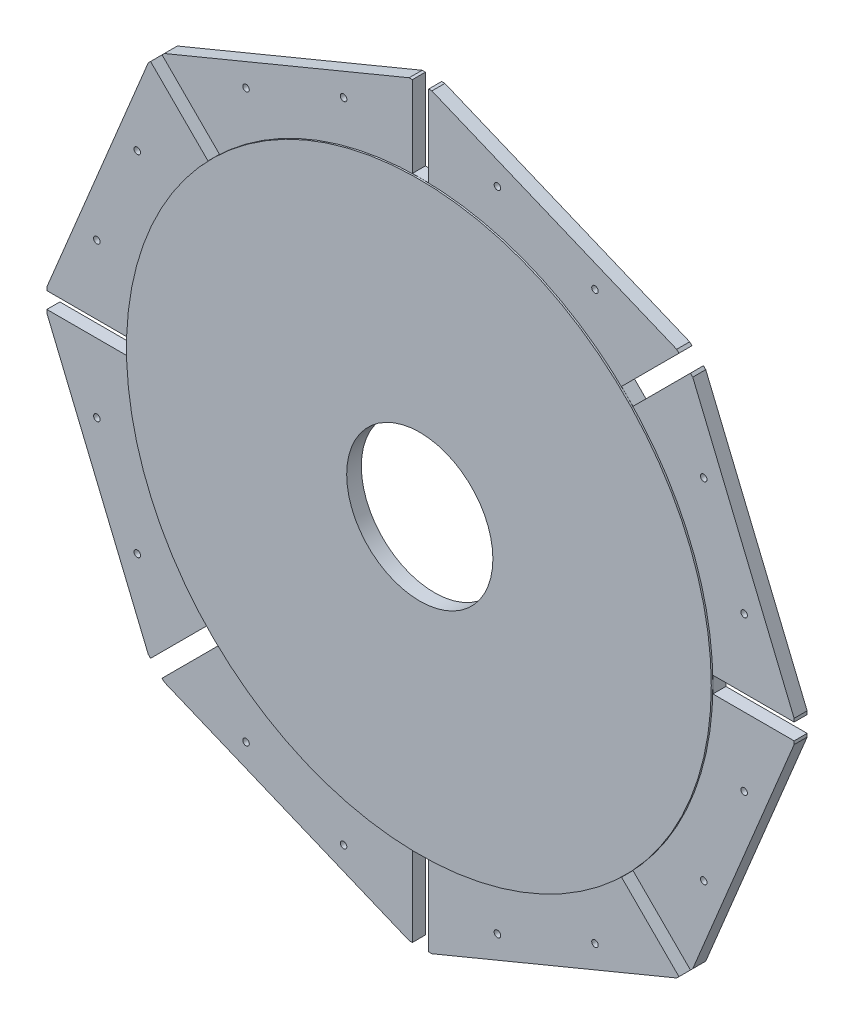
SolidWorks part; units mm, degrees
ref_plane "Front Plane" through (0, 0, 0) normal (0, 0, 1) x (1, 0, 0)
ref_plane "Top Plane" through (0, 0, 0) normal (0, 1, 0) x (1, 0, 0)
ref_plane "Right Plane" through (0, 0, 0) normal (1, 0, 0) x (0, 0, -1)
sketch "Sketch1" plane through (0, 0, 0) normal (0, 0, 1) x (1, 0, 0)
  line L0 (5, 230) -> (5, 180)
  line L1 (5, 180) -> (-5, 180)
  line L2 (-5, 180) -> (-5, 230)
  line L3 (-5, 230) -> (-7, 230)
  line L4 (-7, 230) -> (-157.6848, 167.5843)
  line L5 (-157.6848, 167.5843) -> (-159.099, 166.1701)
  line L6 (-159.099, 166.1701) -> (-123.7437, 130.8148)
  line L7 (-123.7437, 130.8148) -> (-130.8148, 123.7437)
  line L8 (-130.8148, 123.7437) -> (-166.1701, 159.099)
  line L9 (-166.1701, 159.099) -> (-167.5843, 157.6848)
  line L10 (-167.5843, 157.6848) -> (-230, 7)
  line L11 (-230, 7) -> (-230, 5)
  line L12 (-230, 5) -> (-180, 5)
  line L13 (-180, 5) -> (-180, -5)
  line L14 (-180, -5) -> (-230, -5)
  line L15 (-230, -5) -> (-230, -7)
  line L16 (-230, -7) -> (-167.5843, -157.6848)
  line L17 (-167.5843, -157.6848) -> (-166.1701, -159.099)
  line L18 (-166.1701, -159.099) -> (-130.8148, -123.7437)
  line L19 (-130.8148, -123.7437) -> (-123.7437, -130.8148)
  line L20 (-123.7437, -130.8148) -> (-159.099, -166.1701)
  line L21 (-159.099, -166.1701) -> (-157.6848, -167.5843)
  line L22 (-157.6848, -167.5843) -> (-7, -230)
  line L23 (-7, -230) -> (-5, -230)
  line L24 (-5, -230) -> (-5, -180)
  line L25 (-5, -180) -> (5, -180)
  line L26 (5, -180) -> (5, -230)
  line L27 (5, -230) -> (7, -230)
  line L28 (7, -230) -> (157.6848, -167.5843)
  line L29 (157.6848, -167.5843) -> (159.099, -166.1701)
  line L30 (159.099, -166.1701) -> (123.7437, -130.8148)
  line L31 (123.7437, -130.8148) -> (130.8148, -123.7437)
  line L32 (130.8148, -123.7437) -> (166.1701, -159.099)
  line L33 (166.1701, -159.099) -> (167.5843, -157.6848)
  line L34 (167.5843, -157.6848) -> (230, -7)
  line L35 (230, -7) -> (230, -5)
  line L36 (230, -5) -> (180, -5)
  line L37 (180, -5) -> (180, 5)
  line L38 (180, 5) -> (230, 5)
  line L39 (230, 5) -> (230, 7)
  line L40 (230, 7) -> (167.5843, 157.6848)
  line L41 (167.5843, 157.6848) -> (166.1701, 159.099)
  line L42 (166.1701, 159.099) -> (130.8148, 123.7437)
  line L43 (130.8148, 123.7437) -> (123.7437, 130.8148)
  line L44 (123.7437, 130.8148) -> (159.099, 166.1701)
  line L45 (159.099, 166.1701) -> (157.6848, 167.5843)
  line L46 (157.6848, 167.5843) -> (7, 230)
  line L47 (7, 230) -> (5, 230)
  line L48 (0, 180) -> (0, -180) construction
  line L49 (-180, 0) -> (180, 0) construction
  dimension "D1" = 163.1001
  dimension "D2" = 10
extrude "Boss-Extrude1" add sketch "Sketch1" along normal blind 8
sketch "Sketch2" plane through (0, 0, 8) normal (0, 0, 1) x (1, 0, 0)
  line L0 (5, 180) -> (-5, 180) construction
  circle A0 centre (0, 0) radius 180
  point P0 (0, 180)
extrude "Boss-Extrude2" add sketch "Sketch2" along normal blind 1
sketch "Sketch3" plane through (0, 0, 8) normal (0, 0, 1) x (1, 0, 0)
  circle A0 centre (107.3978, 174.3545) radius 2
  circle A1 centre (47.3456, 199.2289) radius 2
  circle A3 centre (199.2289, 47.3456) radius 2
  circle A4 centre (174.3545, 107.3978) radius 2
  circle A5 centre (174.3545, -107.3978) radius 2
  circle A6 centre (199.2289, -47.3456) radius 2
  circle A7 centre (47.3456, -199.2289) radius 2
  circle A8 centre (107.3978, -174.3545) radius 2
  circle A9 centre (-107.3978, -174.3545) radius 2
  circle A10 centre (-47.3456, -199.2289) radius 2
  circle A11 centre (-199.2289, -47.3456) radius 2
  circle A12 centre (-174.3545, -107.3978) radius 2
  circle A13 centre (-174.3545, 107.3978) radius 2
  circle A14 centre (-199.2289, 47.3456) radius 2
  circle A15 centre (-47.3456, 199.2289) radius 2
  circle A16 centre (-107.3978, 174.3545) radius 2
  point P37 (0, 0)
  dimension "D1" = 8
extrude "Cut-Extrude1" cut sketch "Sketch3" against normal up to next
sketch "Sketch4" plane through (0, 0, 0) normal (0, 0, -1) x (-1, 0, 0)
  circle A0 centre (-0.5579, 0.279) radius 45
  dimension "D1" = 90
extrude "Cut-Extrude2" cut sketch "Sketch4" against normal up to next
